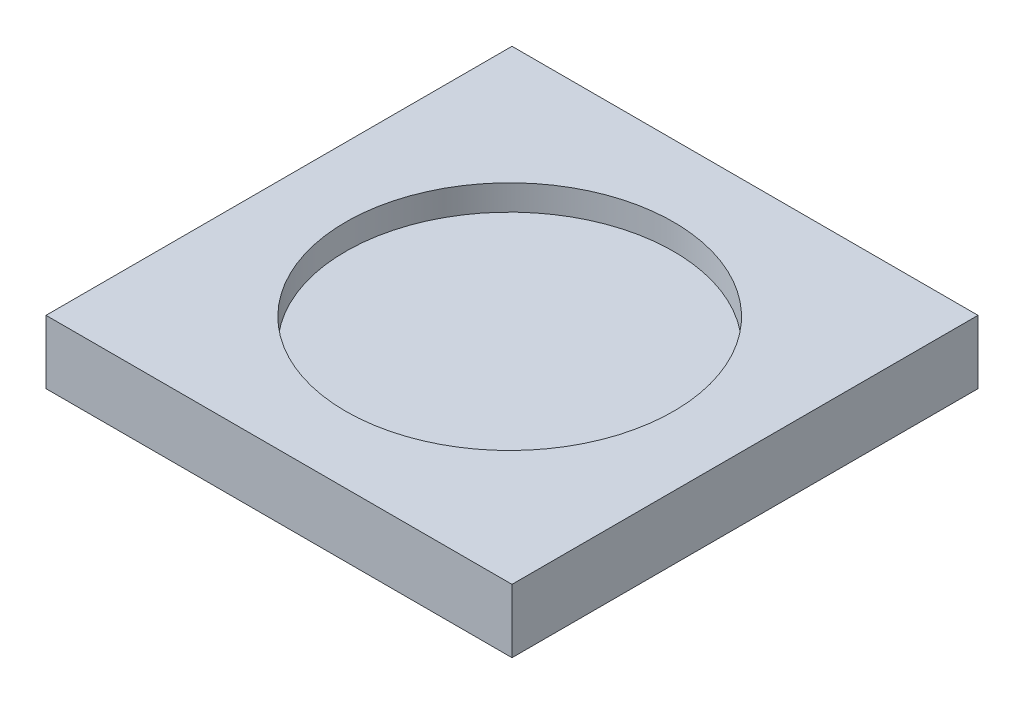
SolidWorks part; units mm, degrees
ref_plane "Front Plane" through (0, 0, 0) normal (0, 0, 1) x (1, 0, 0)
ref_plane "Top Plane" through (0, 0, 0) normal (0, 1, 0) x (1, 0, 0)
ref_plane "Right Plane" through (0, 0, 0) normal (1, 0, 0) x (0, 0, -1)
sketch "Sketch1" plane through (0, 0, 0) normal (0, 1, 0) x (1, 0, 0)
  line L1 (0, 0) -> (-36.6667, 0)
  line L2 (0, 0) -> (0, 36.6667)
  line L3 (0, 36.6667) -> (-36.6667, 36.6667)
  line L4 (-36.6667, 0) -> (-36.6667, 36.6667)
  dimension "D1" = 36.6667
  dimension "D2" = 36.6667
extrude "Boss-Extrude1" add sketch "Sketch1" along normal blind 5
sketch "Sketch2" plane through (0, 5, 0) normal (0, 1, 0) x (1, 0, 0)
  line L0 (-18.3333, 36.6667) -> (-18.3333, -0.3661) construction
  line L1 (0, 36.6667) -> (-36.6667, 36.6667) construction
  circle A0 centre (-18.3333, 18.1503) radius 12.9
  dimension "D1" = 25.8
extrude "Cut-Extrude1" cut sketch "Sketch2" against normal blind 2
